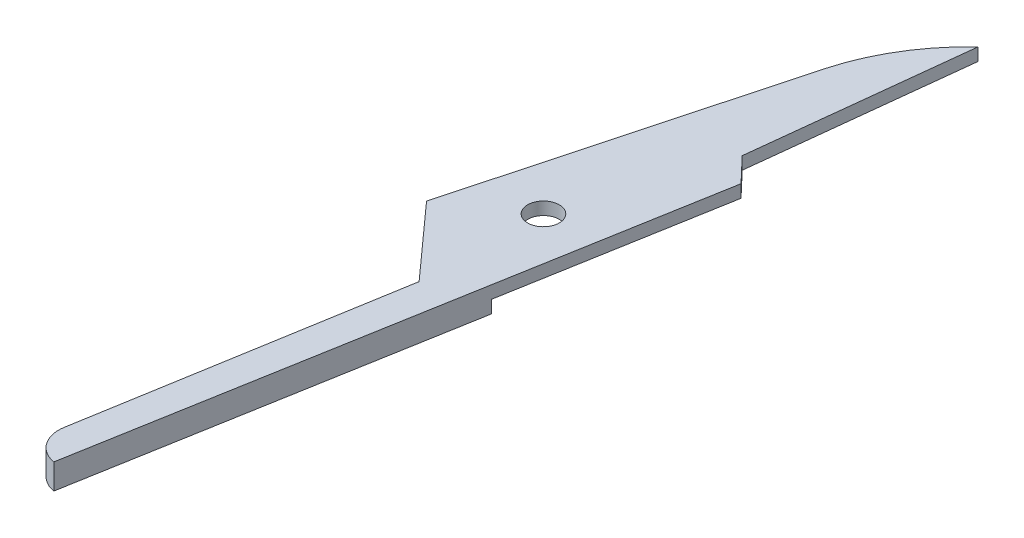
SolidWorks part; units mm, degrees
material "1060 Alloy"
ref_plane "Front Plane" through (0, 0, 0) normal (0, 0, 1) x (1, 0, 0)
ref_plane "Top Plane" through (0, 0, 0) normal (0, 1, 0) x (1, 0, 0)
ref_plane "Right Plane" through (0, 0, 0) normal (1, 0, 0) x (0, 0, -1)
sketch "Sketch1" plane through (0, 0, 0) normal (0, 1, 0) x (1, 0, 0)
  line L1 (0, 0) -> (-9, 0) construction
  line L2 (0, 0) -> (0, 52) construction
  line L3 (0, 52) -> (-9, 52) construction
  line L4 (-9, 0) -> (-9, 52) construction
  line L6 (-9, 26.0941) -> (-3.6753, 45.8905)
  line L7 (0, 52) -> (-1.5, 38.5738)
  line L9 (-9, 26.0941) -> (-4.8224, 21.4455)
  line L10 (-1.5, 38.5738) -> (0, 37)
  line L11 (0, 37) -> (-6.5, 0)
  line L12 (-8.0658, 2.2171) -> (-4.8224, 21.4455)
  arc A1 (-3.6753, 45.8905) -> (0, 52) centre (8.833, 42.5261) cw
  arc A12 (-6.5, 0) -> (-8.0658, 2.2171) centre (-6.1668, 1.8968) cw
  point P6 (-9, 26.0941)
  dimension "D7" = 6.5
  dimension "D8" = 19.5
  dimension "D6" = 1.9258
  dimension "D2" = 12.9529
  dimension "D1" = 9
  dimension "D3" = 13.4262
  dimension "D4" = 52
  dimension "D5" = 6.25
  dimension "D9" = 123
  dimension "D10" = 130
  dimension "D11" = 1.5
  dimension "D13" = 20.5
extrude "Boss-Extrude1" add sketch "Sketch1" along normal blind 1.6
sketch "Sketch2" plane through (0, 1.6, 0) normal (0, 1, 0) x (1, 0, 0)
  circle A0 centre (-4.6, 29.0941) radius 1
  dimension "D1" = 2
  dimension "D2" = 3
  dimension "D3" = 4.4
extrude "Cut-Extrude1" cut sketch "Sketch2" against normal through all
sketch "Sketch4" plane through (0, 0, 0) normal (0, -1, 0) x (1, 0, 0)
  line L0 (-5.441, -22.1339) -> (-15.4552, -22.1339)
  line L1 (-15.4552, -22.1339) -> (-15.4552, -68.1304)
  line L2 (-15.4552, -68.1304) -> (6.6215, -68.1304)
  line L3 (6.6215, -68.1304) -> (6.6215, -27.7587)
  line L4 (6.6215, -27.7587) -> (-5.441, -22.1339)
  line L5 (-9, -26.0941) -> (-4.8224, -21.4455) construction
  line L6 (0, 0) -> (0, -68.1304) construction
  dimension "D1" = 155
  dimension "D2" = 13.3095
  dimension "D3" = 22.0767
  dimension "D4" = 40.3717
  dimension "D5" = 68.1304
extrude "Cut-Extrude2" cut sketch "Sketch4" against normal blind 0.8
